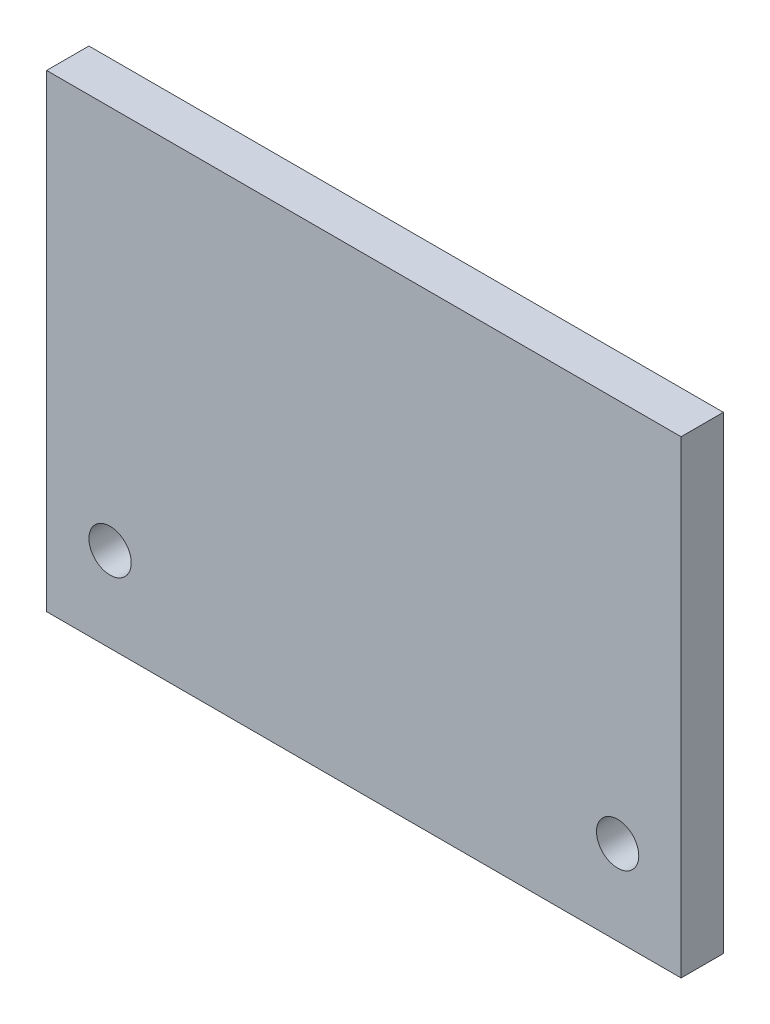
SolidWorks part; units mm, degrees
ref_plane "Front Plane" through (0, 0, 0) normal (0, 0, 1) x (1, 0, 0)
ref_plane "Top Plane" through (0, 0, 0) normal (0, 1, 0) x (1, 0, 0)
ref_plane "Right Plane" through (0, 0, 0) normal (1, 0, 0) x (0, 0, -1)
sketch "Sketch1" plane through (0, 0, 0) normal (0, 0, 1) x (1, 0, 0)
  line L1 (-6.35, 98.5775) -> (88.9, 98.5775)
  line L2 (-6.35, 98.5775) -> (-6.35, 28.203)
  line L3 (-6.35, 28.203) -> (88.9, 28.203)
  line L4 (88.9, 98.5775) -> (88.9, 28.203)
extrude "Boss-Extrude1" add sketch "Sketch1" against normal blind 6.35 contours L1 L4 L3 L2
sketch "Sketch2" plane through (0, 0, 0) normal (0, 0, 1) x (1, 0, 0)
  line L0 (-6.35, 28.203) -> (88.9, 28.203) construction
  line L1 (88.9, 98.5775) -> (88.9, 28.203) construction
  line L2 (-6.35, 98.5775) -> (-6.35, 28.203) construction
  circle A0 centre (79.375, 40.903) radius 3.175
  circle A1 centre (3.175, 40.903) radius 3.175
  dimension "D1" = 12.7
  dimension "D2" = 6.35
  dimension "D3" = 12.7
  dimension "D4" = 6.35
  dimension "D5" = 9.525
  dimension "D6" = 9.525
extrude "Cut-Extrude1" cut sketch "Sketch2" against normal blind 6.35
